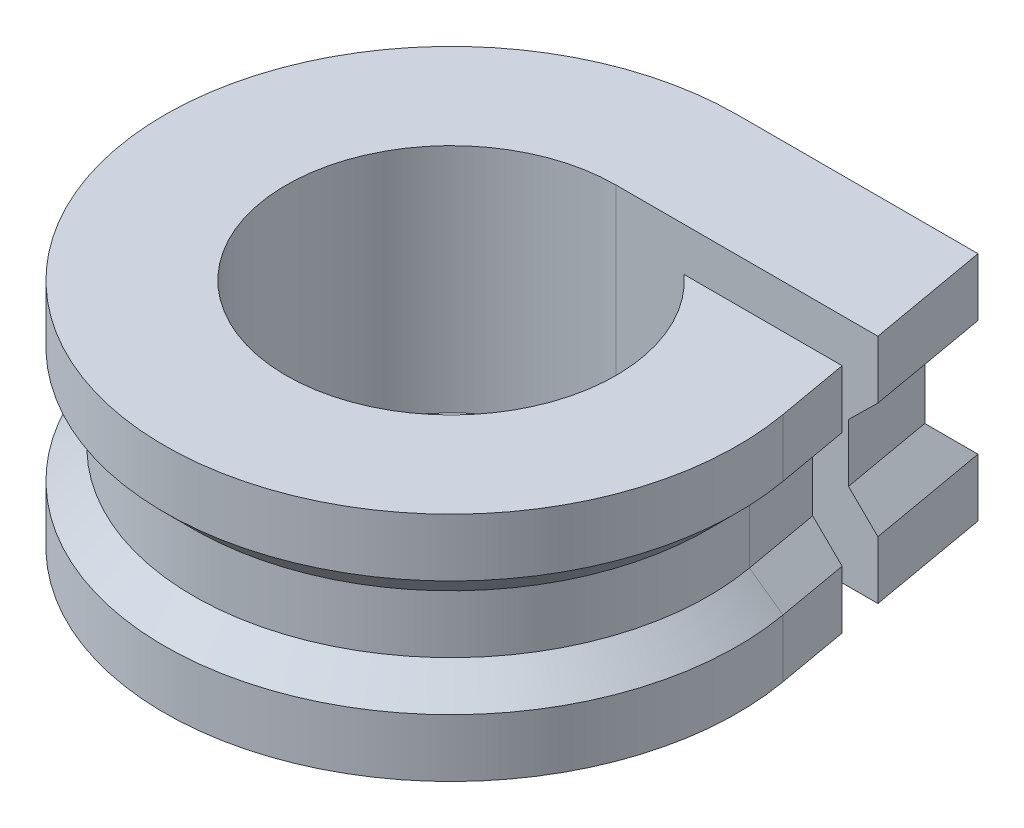
SolidWorks part; units mm, degrees
ref_plane "Front Plane" through (0, 0, 0) normal (0, 0, 1) x (1, 0, 0)
ref_plane "Top Plane" through (0, 0, 0) normal (0, 1, 0) x (1, 0, 0)
ref_plane "Right Plane" through (0, 0, 0) normal (1, 0, 0) x (0, 0, -1)
sketch "Sketch1" plane through (0, 0, 0) normal (0, 1, 0) x (1, 0, 0)
  line L0 (0, 9.9) -> (8.3071, 9.9)
  line L1 (8.3071, 9.9) -> (9.7496, 1.7191)
  line L2 (0, 5.7) -> (9.0477, 5.7)
  line L3 (3.8536, 4.2) -> (9.3122, 4.2)
  circle A0 centre (0, 0) radius 5.7
  arc A1 (0, 9.9) -> (9.7496, 1.7191) centre (0, 0) ccw
  dimension "D1" = 11.4
  dimension "D2" = 4.2
  dimension "D3" = 100
  dimension "D4" = 1.5
extrude "Boss-Extrude1" add sketch "Sketch1" along normal blind 3 contours L0 A1 L1 L3 A0 L2
chamfer "Chamfer1" distance 1 angle 45 4 edges at (4.1535, 3, -9.9) (9.5309, 3, -2.9596) (-6.3636, 3, 7.5838) (8.6774, 3, -7.8)
sketch "Sketch3" plane through (0, 3, 0) normal (0, 1, 0) x (1, 0, 0)
  line L9 (0, 5.7) -> (8.0322, 5.7)
  line L15 (8.0322, 5.7) -> (7.468, 8.9)
  line L16 (7.468, 8.9) -> (0, 8.9)
  line L19 (8.7648, 1.5455) -> (8.2967, 4.2)
  line L20 (8.2967, 4.2) -> (3.8536, 4.2)
  line L21 (0, 5.7) -> (8.0322, 5.7)
  line L22 (8.0322, 5.7) -> (7.468, 8.9)
  line L23 (7.468, 8.9) -> (0, 8.9)
  line L24 (8.7648, 1.5455) -> (8.2967, 4.2)
  line L25 (8.2967, 4.2) -> (3.8536, 4.2)
  arc A6 (0, 8.9) -> (8.7648, 1.5455) centre (0, 0) ccw
  arc A7 (0, 5.7) -> (3.8536, 4.2) centre (0, 0) ccw
  arc A8 (0, 8.9) -> (8.7648, 1.5455) centre (0, 0) ccw
  arc A9 (0, 5.7) -> (3.8536, 4.2) centre (0, 0) ccw
  point P9 (7.6583, 5.4)
  dimension "D1" = 0
extrude "Boss-Extrude2" add sketch "Sketch3" along normal blind 1
mirror "Mirror1" about plane through (0, 4, 0) normal (0, 1, 0) of bodies 102
